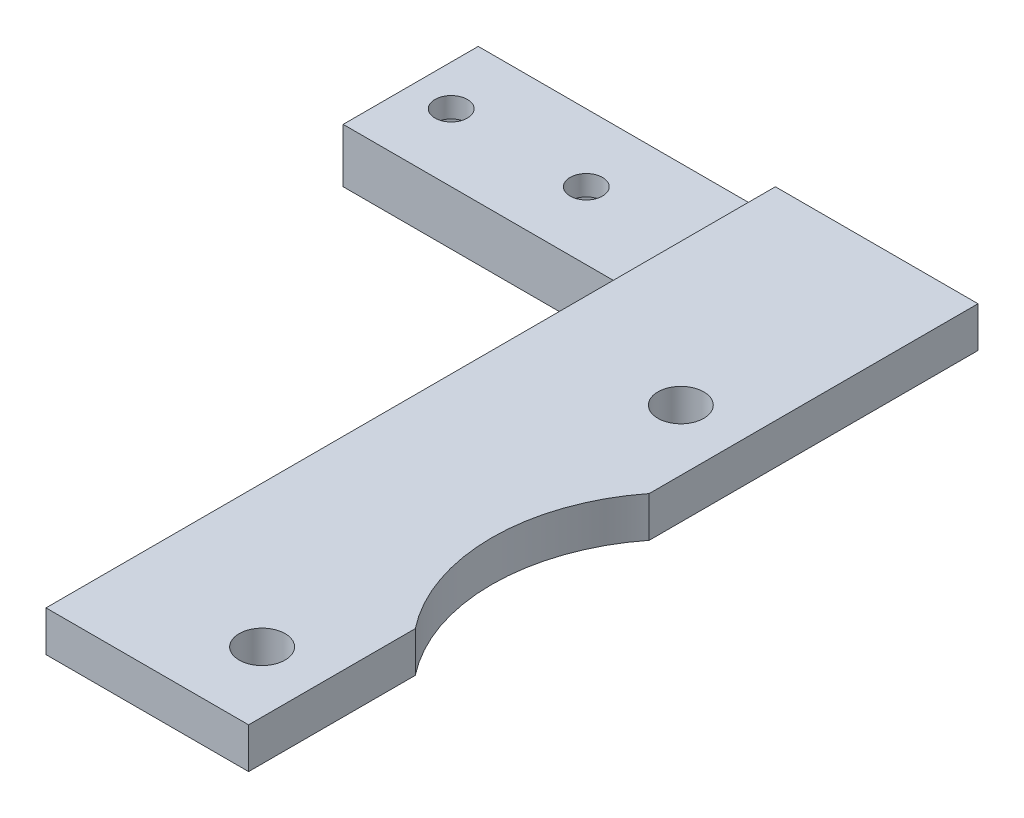
SolidWorks part; units mm, degrees
ref_plane "Alzado" through (0, 0, 0) normal (0, 0, 1) x (1, 0, 0)
ref_plane "Planta" through (0, 0, 0) normal (0, 1, 0) x (1, 0, 0)
ref_plane "Vista lateral" through (0, 0, 0) normal (1, 0, 0) x (0, 0, -1)
sketch "Croquis1" plane through (0, 0, 0) normal (0, 0, 1) x (1, 0, 0)
  line L0 (0, 4) -> (0, 0)
  line L1 (0, 0) -> (24, 0)
  line L2 (25, 1) -> (25, 2)
  line L3 (26, 3) -> (37, 3)
  line L4 (37, 3) -> (37, 6)
  line L5 (37, 6) -> (22, 6)
  line L6 (0, 4) -> (21, 4)
  line L7 (22, 5) -> (22, 6)
  arc A0 (22, 5) -> (21, 4) centre (21, 5) cw
  arc A1 (25, 2) -> (26, 3) centre (26, 2) cw
  arc A2 (25, 1) -> (24, 0) centre (24, 1) cw
  point P14 (0, 0)
  dimension "D1" = 1
  dimension "D2" = 15
  dimension "D3" = 1
  dimension "D4" = 3
  dimension "D5" = 11
  dimension "D6" = 4
  dimension "D7" = 24
extrude "Saliente-Extruir1" add sketch "Croquis1" along normal blind 10
sketch "Croquis2" plane through (0, 0, 10) normal (0, 0, 1) x (1, 0, 0)
  line L1 (37, 3) -> (22, 3)
  line L2 (37, 3) -> (37, 6)
  line L3 (37, 6) -> (22, 6)
  line L4 (22, 3) -> (22, 6)
  point P4 (0, 0)
  point P6 (0, 0)
  point P9 (0, 0)
  point P10 (0, 0)
extrude "Saliente-Extruir2" add sketch "Croquis2" along normal blind 44
sketch "Croquis3" plane through (0, 6, 0) normal (0, 1, 0) x (1, 0, 0)
  line L0 (37, 0) -> (22, 0) construction
  line L1 (37, -54) -> (37, 0) construction
  circle A0 centre (48, -33) radius 14
  circle A1 centre (32.5, -17.5) radius 1.7
  circle A2 centre (32.5, -48.5) radius 1.7
  point P6 (0, 0)
  dimension "D4" = 3.4
  dimension "D5" = 28
  dimension "D1" = 15.5
  dimension "D2" = 15.5
  dimension "D3" = 15.5
  dimension "D6" = 33
  dimension "D7" = 11
extrude "Cortar-Extruir1" cut sketch "Croquis3" against normal blind 44
sketch "Croquis4" plane through (0, 4, 0) normal (0, 1, 0) x (1, 0, 0)
  circle A0 centre (13, -5) radius 1.2
  circle A1 centre (3, -5) radius 1.2
  point P4 (0, 0)
  dimension "D4" = 2.4
  dimension "D1" = 5
  dimension "D2" = 3
  dimension "D3" = 10
extrude "Cortar-Extruir2" cut sketch "Croquis4" against normal blind 5
sketch "Croquis5" plane through (0, 0, 0) normal (0, -1, 0) x (1, 0, 0)
  line L0 (0, 10) -> (0, 0) construction
  line L1 (3, 7.25) -> (1.0514, 6.125)
  line L2 (1.0514, 6.125) -> (1.0514, 3.875)
  line L3 (1.0514, 3.875) -> (3, 2.75)
  line L4 (3, 2.75) -> (4.9486, 3.875)
  line L5 (4.9486, 3.875) -> (4.9486, 6.125)
  line L6 (4.9486, 6.125) -> (3, 7.25)
  line L7 (13, 7.25) -> (11.0514, 6.125)
  line L8 (11.0514, 6.125) -> (11.0514, 3.875)
  line L9 (11.0514, 3.875) -> (13, 2.75)
  line L10 (13, 2.75) -> (14.9486, 3.875)
  line L11 (14.9486, 3.875) -> (14.9486, 6.125)
  line L12 (14.9486, 6.125) -> (13, 7.25)
  circle A0 centre (3, 5) radius 2.25 construction
  circle A1 centre (13, 5) radius 2.25 construction
  dimension "D1" = 4.5
extrude "Cortar-Extruir3" cut sketch "Croquis5" against normal blind 2.5
